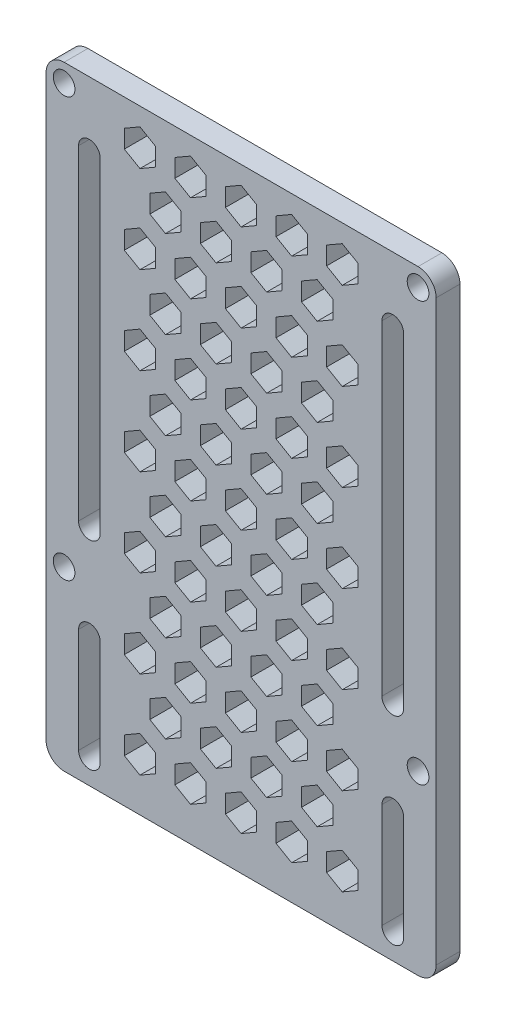
SolidWorks part; units mm, degrees
ref_plane "前基準面" through (0, 0, 0) normal (0, 0, 1) x (1, 0, 0)
ref_plane "上基準面" through (0, 0, 0) normal (0, 1, 0) x (1, 0, 0)
ref_plane "右基準面" through (0, 0, 0) normal (1, 0, 0) x (0, 0, -1)
sketch "草圖1" plane through (0, 0, 0) normal (0, 0, 1) x (1, 0, 0)
  line L0 (-16.3018, 23.2899) -> (-16.3018, -21.7101) construction
  line L1 (-19.8018, 29.7899) -> (29.1982, 29.7899) construction
  line L2 (-19.8018, 29.7899) -> (-19.8018, -28.2101) construction
  line L3 (-19.8018, -28.2101) -> (29.1982, -28.2101) construction
  line L4 (29.1982, 29.7899) -> (29.1982, -28.2101) construction
  line L5 (4.6982, 29.7899) -> (4.6982, 10.4942) construction
  line L6 (-20.7626, 0.7899) -> (-12.2996, 0.7899) construction
  line L7 (-16.3018, 29.7899) -> (-16.3018, 22.2296) construction
  line L8 (25.6982, 29.7899) -> (25.6982, 22.2296) construction
  line L9 (-14.8018, 23.2899) -> (-14.8018, -21.7101)
  line L10 (-17.8018, 23.2899) -> (-17.8018, -21.7101)
  line L11 (25.6982, 23.2899) -> (25.6982, -21.7101) construction
  line L12 (24.1982, 23.2899) -> (24.1982, -21.7101)
  line L13 (27.1982, 23.2899) -> (27.1982, -21.7101)
  line L14 (-19.8018, 32.2899) -> (29.1982, 32.2899)
  line L15 (-22.3018, 29.7899) -> (-22.3018, -28.2101)
  line L16 (31.6982, 29.7899) -> (31.6982, -28.2101)
  line L17 (-22.3018, -28.2101) -> (-22.3018, -50.2101)
  line L18 (-19.8018, -52.7101) -> (29.1982, -52.7101)
  line L19 (31.6982, -28.2101) -> (31.6982, -50.2101)
  line L20 (-16.3018, -34.7101) -> (-16.3018, -49.2101) construction
  line L21 (-14.8018, -34.7101) -> (-14.8018, -49.2101)
  line L22 (-17.8018, -34.7101) -> (-17.8018, -49.2101)
  line L23 (25.6982, -34.7101) -> (25.6982, -49.2101) construction
  line L24 (24.1982, -34.7101) -> (24.1982, -49.2101)
  line L25 (27.1982, -34.7101) -> (27.1982, -49.2101)
  line L26 (4.6982, 27.2899) -> (12.1639, 27.2899) construction
  line L27 (6.8632, 28.5399) -> (4.6982, 29.7899)
  line L28 (4.6982, 29.7899) -> (2.5331, 28.5399)
  line L29 (2.5331, 28.5399) -> (2.5331, 26.0399)
  line L30 (2.5331, 26.0399) -> (4.6982, 24.7899)
  line L31 (4.6982, 24.7899) -> (6.8632, 26.0399)
  line L32 (6.8632, 26.0399) -> (6.8632, 28.5399)
  line L33 (13.8632, 28.5399) -> (11.6982, 29.7899)
  line L34 (11.6982, 29.7899) -> (9.5331, 28.5399)
  line L35 (9.5331, 28.5399) -> (9.5331, 26.0399)
  line L36 (9.5331, 26.0399) -> (11.6982, 24.7899)
  line L37 (11.6982, 24.7899) -> (13.8632, 26.0399)
  line L38 (13.8632, 26.0399) -> (13.8632, 28.5399)
  line L39 (20.8632, 28.5399) -> (18.6982, 29.7899)
  line L40 (18.6982, 29.7899) -> (16.5331, 28.5399)
  line L41 (16.5331, 28.5399) -> (16.5331, 26.0399)
  line L42 (16.5331, 26.0399) -> (18.6982, 24.7899)
  line L43 (18.6982, 24.7899) -> (20.8632, 26.0399)
  line L44 (20.8632, 26.0399) -> (20.8632, 28.5399)
  line L45 (-0.1368, 28.5399) -> (-2.3018, 29.7899)
  line L46 (-2.3018, 29.7899) -> (-4.4669, 28.5399)
  line L47 (-4.4669, 28.5399) -> (-4.4669, 26.0399)
  line L48 (-4.4669, 26.0399) -> (-2.3018, 24.7899)
  line L49 (-2.3018, 24.7899) -> (-0.1368, 26.0399)
  line L50 (-0.1368, 26.0399) -> (-0.1368, 28.5399)
  line L51 (-7.1368, 28.5399) -> (-9.3018, 29.7899)
  line L52 (-9.3018, 29.7899) -> (-11.4669, 28.5399)
  line L53 (-11.4669, 28.5399) -> (-11.4669, 26.0399)
  line L54 (-11.4669, 26.0399) -> (-9.3018, 24.7899)
  line L55 (-9.3018, 24.7899) -> (-7.1368, 26.0399)
  line L56 (-7.1368, 26.0399) -> (-7.1368, 28.5399)
  line L57 (-2.3018, 24.7899) -> (4.6982, 24.7899) construction
  line L58 (1.229, 24.4101) -> (1.229, 20.9719) construction
  line L59 (10.3941, 19.9954) -> (10.3941, 22.4954)
  line L60 (3.3941, 19.9954) -> (3.3941, 22.4954)
  line L61 (3.3941, 22.4954) -> (1.229, 23.7454)
  line L62 (1.229, 23.7454) -> (-0.936, 22.4954)
  line L63 (-0.936, 22.4954) -> (-0.936, 19.9954)
  line L64 (-0.936, 19.9954) -> (1.229, 18.7454)
  line L65 (1.229, 18.7454) -> (3.3941, 19.9954)
  line L66 (10.3941, 22.4954) -> (8.229, 23.7454)
  line L67 (8.229, 23.7454) -> (6.064, 22.4954)
  line L68 (6.064, 22.4954) -> (6.064, 19.9954)
  line L69 (6.064, 19.9954) -> (8.229, 18.7454)
  line L70 (8.229, 18.7454) -> (10.3941, 19.9954)
  line L71 (17.3941, 19.9954) -> (17.3941, 22.4954)
  line L72 (17.3941, 22.4954) -> (15.229, 23.7454)
  line L73 (15.229, 23.7454) -> (13.064, 22.4954)
  line L74 (13.064, 22.4954) -> (13.064, 19.9954)
  line L75 (13.064, 19.9954) -> (15.229, 18.7454)
  line L76 (15.229, 18.7454) -> (17.3941, 19.9954)
  line L77 (-3.6059, 20.0151) -> (-3.6059, 22.5151)
  line L78 (-3.6059, 22.5151) -> (-5.7709, 23.7651)
  line L79 (-5.7709, 23.7651) -> (-7.936, 22.5151)
  line L80 (-7.936, 22.5151) -> (-7.936, 20.0151)
  line L81 (-7.936, 20.0151) -> (-5.7709, 18.7651)
  line L82 (-5.7709, 18.7651) -> (-3.6059, 20.0151)
  line L83 (-7.1368, 16.4152) -> (-9.3018, 17.6652)
  line L84 (-9.3018, 17.6652) -> (-11.4669, 16.4152)
  line L85 (-11.4669, 16.4152) -> (-11.4669, 13.9152)
  line L86 (-11.4669, 13.9152) -> (-9.3018, 12.6652)
  line L87 (-9.3018, 12.6652) -> (-7.1368, 13.9152)
  line L88 (-7.1368, 13.9152) -> (-7.1368, 16.4152)
  line L89 (-3.6059, 7.8905) -> (-3.6059, 10.3905)
  line L90 (-3.6059, 10.3905) -> (-5.7709, 11.6405)
  line L91 (-5.7709, 11.6405) -> (-7.936, 10.3905)
  line L92 (-7.936, 10.3905) -> (-7.936, 7.8905)
  line L93 (-7.936, 7.8905) -> (-5.7709, 6.6405)
  line L94 (-5.7709, 6.6405) -> (-3.6059, 7.8905)
  line L95 (-0.1368, 16.4152) -> (-2.3018, 17.6652)
  line L96 (-2.3018, 17.6652) -> (-4.4669, 16.4152)
  line L97 (-4.4669, 16.4152) -> (-4.4669, 13.9152)
  line L98 (-4.4669, 13.9152) -> (-2.3018, 12.6652)
  line L99 (-2.3018, 12.6652) -> (-0.1368, 13.9152)
  line L100 (-0.1368, 13.9152) -> (-0.1368, 16.4152)
  line L101 (3.3941, 7.8707) -> (3.3941, 10.3707)
  line L102 (3.3941, 10.3707) -> (1.229, 11.6207)
  line L103 (1.229, 11.6207) -> (-0.936, 10.3707)
  line L104 (-0.936, 10.3707) -> (-0.936, 7.8707)
  line L105 (-0.936, 7.8707) -> (1.229, 6.6207)
  line L106 (1.229, 6.6207) -> (3.3941, 7.8707)
  line L107 (6.8632, 16.4152) -> (4.6982, 17.6652)
  line L108 (4.6982, 17.6652) -> (2.5331, 16.4152)
  line L109 (2.5331, 16.4152) -> (2.5331, 13.9152)
  line L110 (2.5331, 13.9152) -> (4.6982, 12.6652)
  line L111 (4.6982, 12.6652) -> (6.8632, 13.9152)
  line L112 (6.8632, 13.9152) -> (6.8632, 16.4152)
  line L113 (13.8632, 16.4152) -> (11.6982, 17.6652)
  line L114 (11.6982, 17.6652) -> (9.5331, 16.4152)
  line L115 (9.5331, 16.4152) -> (9.5331, 13.9152)
  line L116 (9.5331, 13.9152) -> (11.6982, 12.6652)
  line L117 (11.6982, 12.6652) -> (13.8632, 13.9152)
  line L118 (13.8632, 13.9152) -> (13.8632, 16.4152)
  line L119 (20.8632, 16.4152) -> (18.6982, 17.6652)
  line L120 (18.6982, 17.6652) -> (16.5331, 16.4152)
  line L121 (16.5331, 16.4152) -> (16.5331, 13.9152)
  line L122 (16.5331, 13.9152) -> (18.6982, 12.6652)
  line L123 (18.6982, 12.6652) -> (20.8632, 13.9152)
  line L124 (20.8632, 13.9152) -> (20.8632, 16.4152)
  line L125 (17.3941, 7.8707) -> (17.3941, 10.3707)
  line L126 (17.3941, 10.3707) -> (15.229, 11.6207)
  line L127 (15.229, 11.6207) -> (13.064, 10.3707)
  line L128 (13.064, 10.3707) -> (13.064, 7.8707)
  line L129 (13.064, 7.8707) -> (15.229, 6.6207)
  line L130 (15.229, 6.6207) -> (17.3941, 7.8707)
  line L131 (10.3941, 7.8707) -> (10.3941, 10.3707)
  line L132 (10.3941, 10.3707) -> (8.229, 11.6207)
  line L133 (8.229, 11.6207) -> (6.064, 10.3707)
  line L134 (6.064, 10.3707) -> (6.064, 7.8707)
  line L135 (6.064, 7.8707) -> (8.229, 6.6207)
  line L136 (8.229, 6.6207) -> (10.3941, 7.8707)
  line L137 (-3.6059, -4.2295) -> (-3.6059, -1.7295)
  line L138 (-3.6059, -1.7295) -> (-5.7709, -0.4795)
  line L139 (-5.7709, -0.4795) -> (-7.936, -1.7295)
  line L140 (-7.936, -1.7295) -> (-7.936, -4.2295)
  line L141 (-7.936, -4.2295) -> (-5.7709, -5.4795)
  line L142 (-5.7709, -5.4795) -> (-3.6059, -4.2295)
  line L143 (-7.1368, 4.2952) -> (-9.3018, 5.5452)
  line L144 (-9.3018, 5.5452) -> (-11.4669, 4.2952)
  line L145 (-11.4669, 4.2952) -> (-11.4669, 1.7952)
  line L146 (-11.4669, 1.7952) -> (-9.3018, 0.5452)
  line L147 (-9.3018, 0.5452) -> (-7.1368, 1.7952)
  line L148 (-7.1368, 1.7952) -> (-7.1368, 4.2952)
  line L149 (-0.1368, 4.2952) -> (-2.3018, 5.5452)
  line L150 (-2.3018, 5.5452) -> (-4.4669, 4.2952)
  line L151 (-4.4669, 4.2952) -> (-4.4669, 1.7952)
  line L152 (-4.4669, 1.7952) -> (-2.3018, 0.5452)
  line L153 (-2.3018, 0.5452) -> (-0.1368, 1.7952)
  line L154 (-0.1368, 1.7952) -> (-0.1368, 4.2952)
  line L155 (3.3941, -4.2493) -> (3.3941, -1.7493)
  line L156 (3.3941, -1.7493) -> (1.229, -0.4993)
  line L157 (1.229, -0.4993) -> (-0.936, -1.7493)
  line L158 (-0.936, -1.7493) -> (-0.936, -4.2493)
  line L159 (-0.936, -4.2493) -> (1.229, -5.4993)
  line L160 (1.229, -5.4993) -> (3.3941, -4.2493)
  line L161 (10.3941, -4.2493) -> (10.3941, -1.7493)
  line L162 (10.3941, -1.7493) -> (8.229, -0.4993)
  line L163 (8.229, -0.4993) -> (6.064, -1.7493)
  line L164 (6.064, -1.7493) -> (6.064, -4.2493)
  line L165 (6.064, -4.2493) -> (8.229, -5.4993)
  line L166 (8.229, -5.4993) -> (10.3941, -4.2493)
  line L167 (6.8632, 4.2952) -> (4.6982, 5.5452)
  line L168 (4.6982, 5.5452) -> (2.5331, 4.2952)
  line L169 (2.5331, 4.2952) -> (2.5331, 1.7952)
  line L170 (2.5331, 1.7952) -> (4.6982, 0.5452)
  line L171 (4.6982, 0.5452) -> (6.8632, 1.7952)
  line L172 (6.8632, 1.7952) -> (6.8632, 4.2952)
  line L173 (13.8632, 4.2952) -> (11.6982, 5.5452)
  line L174 (11.6982, 5.5452) -> (9.5331, 4.2952)
  line L175 (9.5331, 4.2952) -> (9.5331, 1.7952)
  line L176 (9.5331, 1.7952) -> (11.6982, 0.5452)
  line L177 (11.6982, 0.5452) -> (13.8632, 1.7952)
  line L178 (13.8632, 1.7952) -> (13.8632, 4.2952)
  line L179 (20.8632, 4.2952) -> (18.6982, 5.5452)
  line L180 (18.6982, 5.5452) -> (16.5331, 4.2952)
  line L181 (16.5331, 4.2952) -> (16.5331, 1.7952)
  line L182 (16.5331, 1.7952) -> (18.6982, 0.5452)
  line L183 (18.6982, 0.5452) -> (20.8632, 1.7952)
  line L184 (20.8632, 1.7952) -> (20.8632, 4.2952)
  line L185 (17.3941, -4.2493) -> (17.3941, -1.7493)
  line L186 (17.3941, -1.7493) -> (15.229, -0.4993)
  line L187 (15.229, -0.4993) -> (13.064, -1.7493)
  line L188 (13.064, -1.7493) -> (13.064, -4.2493)
  line L189 (13.064, -4.2493) -> (15.229, -5.4993)
  line L190 (15.229, -5.4993) -> (17.3941, -4.2493)
  line L191 (-3.6059, -16.3495) -> (-3.6059, -13.8495)
  line L192 (-3.6059, -13.8495) -> (-5.7709, -12.5995)
  line L193 (-5.7709, -12.5995) -> (-7.936, -13.8495)
  line L194 (-7.936, -13.8495) -> (-7.936, -16.3495)
  line L195 (-7.936, -16.3495) -> (-5.7709, -17.5995)
  line L196 (-5.7709, -17.5995) -> (-3.6059, -16.3495)
  line L197 (-7.1368, -7.8248) -> (-9.3018, -6.5748)
  line L198 (-9.3018, -6.5748) -> (-11.4669, -7.8248)
  line L199 (-11.4669, -7.8248) -> (-11.4669, -10.3248)
  line L200 (-11.4669, -10.3248) -> (-9.3018, -11.5748)
  line L201 (-9.3018, -11.5748) -> (-7.1368, -10.3248)
  line L202 (-7.1368, -10.3248) -> (-7.1368, -7.8248)
  line L203 (-0.1368, -7.8248) -> (-2.3018, -6.5748)
  line L204 (-2.3018, -6.5748) -> (-4.4669, -7.8248)
  line L205 (-4.4669, -7.8248) -> (-4.4669, -10.3248)
  line L206 (-4.4669, -10.3248) -> (-2.3018, -11.5748)
  line L207 (-2.3018, -11.5748) -> (-0.1368, -10.3248)
  line L208 (-0.1368, -10.3248) -> (-0.1368, -7.8248)
  line L209 (3.3941, -16.3693) -> (3.3941, -13.8693)
  line L210 (3.3941, -13.8693) -> (1.229, -12.6193)
  line L211 (1.229, -12.6193) -> (-0.936, -13.8693)
  line L212 (-0.936, -13.8693) -> (-0.936, -16.3693)
  line L213 (-0.936, -16.3693) -> (1.229, -17.6193)
  line L214 (1.229, -17.6193) -> (3.3941, -16.3693)
  line L215 (10.3941, -16.3693) -> (10.3941, -13.8693)
  line L216 (10.3941, -13.8693) -> (8.229, -12.6193)
  line L217 (8.229, -12.6193) -> (6.064, -13.8693)
  line L218 (6.064, -13.8693) -> (6.064, -16.3693)
  line L219 (6.064, -16.3693) -> (8.229, -17.6193)
  line L220 (8.229, -17.6193) -> (10.3941, -16.3693)
  line L221 (6.8632, -7.8248) -> (4.6982, -6.5748)
  line L222 (4.6982, -6.5748) -> (2.5331, -7.8248)
  line L223 (2.5331, -7.8248) -> (2.5331, -10.3248)
  line L224 (2.5331, -10.3248) -> (4.6982, -11.5748)
  line L225 (4.6982, -11.5748) -> (6.8632, -10.3248)
  line L226 (6.8632, -10.3248) -> (6.8632, -7.8248)
  line L227 (13.8632, -7.8248) -> (11.6982, -6.5748)
  line L228 (11.6982, -6.5748) -> (9.5331, -7.8248)
  line L229 (9.5331, -7.8248) -> (9.5331, -10.3248)
  line L230 (9.5331, -10.3248) -> (11.6982, -11.5748)
  line L231 (11.6982, -11.5748) -> (13.8632, -10.3248)
  line L232 (13.8632, -10.3248) -> (13.8632, -7.8248)
  line L233 (20.8632, -7.8248) -> (18.6982, -6.5748)
  line L234 (18.6982, -6.5748) -> (16.5331, -7.8248)
  line L235 (16.5331, -7.8248) -> (16.5331, -10.3248)
  line L236 (16.5331, -10.3248) -> (18.6982, -11.5748)
  line L237 (18.6982, -11.5748) -> (20.8632, -10.3248)
  line L238 (20.8632, -10.3248) -> (20.8632, -7.8248)
  line L239 (17.3941, -16.3693) -> (17.3941, -13.8693)
  line L240 (17.3941, -13.8693) -> (15.229, -12.6193)
  line L241 (15.229, -12.6193) -> (13.064, -13.8693)
  line L242 (13.064, -13.8693) -> (13.064, -16.3693)
  line L243 (13.064, -16.3693) -> (15.229, -17.6193)
  line L244 (15.229, -17.6193) -> (17.3941, -16.3693)
  line L245 (-3.6059, -28.4695) -> (-3.6059, -25.9695)
  line L246 (-3.6059, -25.9695) -> (-5.7709, -24.7195)
  line L247 (-5.7709, -24.7195) -> (-7.936, -25.9695)
  line L248 (-7.936, -25.9695) -> (-7.936, -28.4695)
  line L249 (-7.936, -28.4695) -> (-5.7709, -29.7195)
  line L250 (-5.7709, -29.7195) -> (-3.6059, -28.4695)
  line L251 (-7.1368, -19.9448) -> (-9.3018, -18.6948)
  line L252 (-9.3018, -18.6948) -> (-11.4669, -19.9448)
  line L253 (-11.4669, -19.9448) -> (-11.4669, -22.4448)
  line L254 (-11.4669, -22.4448) -> (-9.3018, -23.6948)
  line L255 (-9.3018, -23.6948) -> (-7.1368, -22.4448)
  line L256 (-7.1368, -22.4448) -> (-7.1368, -19.9448)
  line L257 (-0.1368, -19.9448) -> (-2.3018, -18.6948)
  line L258 (-2.3018, -18.6948) -> (-4.4669, -19.9448)
  line L259 (-4.4669, -19.9448) -> (-4.4669, -22.4448)
  line L260 (-4.4669, -22.4448) -> (-2.3018, -23.6948)
  line L261 (-2.3018, -23.6948) -> (-0.1368, -22.4448)
  line L262 (-0.1368, -22.4448) -> (-0.1368, -19.9448)
  line L263 (3.3941, -28.4893) -> (3.3941, -25.9893)
  line L264 (3.3941, -25.9893) -> (1.229, -24.7393)
  line L265 (1.229, -24.7393) -> (-0.936, -25.9893)
  line L266 (-0.936, -25.9893) -> (-0.936, -28.4893)
  line L267 (-0.936, -28.4893) -> (1.229, -29.7393)
  line L268 (1.229, -29.7393) -> (3.3941, -28.4893)
  line L269 (10.3941, -28.4893) -> (10.3941, -25.9893)
  line L270 (10.3941, -25.9893) -> (8.229, -24.7393)
  line L271 (8.229, -24.7393) -> (6.064, -25.9893)
  line L272 (6.064, -25.9893) -> (6.064, -28.4893)
  line L273 (6.064, -28.4893) -> (8.229, -29.7393)
  line L274 (8.229, -29.7393) -> (10.3941, -28.4893)
  line L275 (6.8632, -19.9448) -> (4.6982, -18.6948)
  line L276 (4.6982, -18.6948) -> (2.5331, -19.9448)
  line L277 (2.5331, -19.9448) -> (2.5331, -22.4448)
  line L278 (2.5331, -22.4448) -> (4.6982, -23.6948)
  line L279 (4.6982, -23.6948) -> (6.8632, -22.4448)
  line L280 (6.8632, -22.4448) -> (6.8632, -19.9448)
  line L281 (13.8632, -19.9448) -> (11.6982, -18.6948)
  line L282 (11.6982, -18.6948) -> (9.5331, -19.9448)
  line L283 (9.5331, -19.9448) -> (9.5331, -22.4448)
  line L284 (9.5331, -22.4448) -> (11.6982, -23.6948)
  line L285 (11.6982, -23.6948) -> (13.8632, -22.4448)
  line L286 (13.8632, -22.4448) -> (13.8632, -19.9448)
  line L287 (20.8632, -19.9448) -> (18.6982, -18.6948)
  line L288 (18.6982, -18.6948) -> (16.5331, -19.9448)
  line L289 (16.5331, -19.9448) -> (16.5331, -22.4448)
  line L290 (16.5331, -22.4448) -> (18.6982, -23.6948)
  line L291 (18.6982, -23.6948) -> (20.8632, -22.4448)
  line L292 (20.8632, -22.4448) -> (20.8632, -19.9448)
  line L293 (17.3941, -28.4893) -> (17.3941, -25.9893)
  line L294 (17.3941, -25.9893) -> (15.229, -24.7393)
  line L295 (15.229, -24.7393) -> (13.064, -25.9893)
  line L296 (13.064, -25.9893) -> (13.064, -28.4893)
  line L297 (13.064, -28.4893) -> (15.229, -29.7393)
  line L298 (15.229, -29.7393) -> (17.3941, -28.4893)
  line L299 (-3.6059, -40.5895) -> (-3.6059, -38.0895)
  line L300 (-3.6059, -38.0895) -> (-5.7709, -36.8395)
  line L301 (-5.7709, -36.8395) -> (-7.936, -38.0895)
  line L302 (-7.936, -38.0895) -> (-7.936, -40.5895)
  line L303 (-7.936, -40.5895) -> (-5.7709, -41.8395)
  line L304 (-5.7709, -41.8395) -> (-3.6059, -40.5895)
  line L305 (-7.1368, -32.0648) -> (-9.3018, -30.8148)
  line L306 (-9.3018, -30.8148) -> (-11.4669, -32.0648)
  line L307 (-11.4669, -32.0648) -> (-11.4669, -34.5648)
  line L308 (-11.4669, -34.5648) -> (-9.3018, -35.8148)
  line L309 (-9.3018, -35.8148) -> (-7.1368, -34.5648)
  line L310 (-7.1368, -34.5648) -> (-7.1368, -32.0648)
  line L311 (-0.1368, -32.0648) -> (-2.3018, -30.8148)
  line L312 (-2.3018, -30.8148) -> (-4.4669, -32.0648)
  line L313 (-4.4669, -32.0648) -> (-4.4669, -34.5648)
  line L314 (-4.4669, -34.5648) -> (-2.3018, -35.8148)
  line L315 (-2.3018, -35.8148) -> (-0.1368, -34.5648)
  line L316 (-0.1368, -34.5648) -> (-0.1368, -32.0648)
  line L317 (3.3941, -40.6093) -> (3.3941, -38.1093)
  line L318 (3.3941, -38.1093) -> (1.229, -36.8593)
  line L319 (1.229, -36.8593) -> (-0.936, -38.1093)
  line L320 (-0.936, -38.1093) -> (-0.936, -40.6093)
  line L321 (-0.936, -40.6093) -> (1.229, -41.8593)
  line L322 (1.229, -41.8593) -> (3.3941, -40.6093)
  line L323 (10.3941, -40.6093) -> (10.3941, -38.1093)
  line L324 (10.3941, -38.1093) -> (8.229, -36.8593)
  line L325 (8.229, -36.8593) -> (6.064, -38.1093)
  line L326 (6.064, -38.1093) -> (6.064, -40.6093)
  line L327 (6.064, -40.6093) -> (8.229, -41.8593)
  line L328 (8.229, -41.8593) -> (10.3941, -40.6093)
  line L329 (6.8632, -32.0648) -> (4.6982, -30.8148)
  line L330 (4.6982, -30.8148) -> (2.5331, -32.0648)
  line L331 (2.5331, -32.0648) -> (2.5331, -34.5648)
  line L332 (2.5331, -34.5648) -> (4.6982, -35.8148)
  line L333 (4.6982, -35.8148) -> (6.8632, -34.5648)
  line L334 (6.8632, -34.5648) -> (6.8632, -32.0648)
  line L335 (13.8632, -32.0648) -> (11.6982, -30.8148)
  line L336 (11.6982, -30.8148) -> (9.5331, -32.0648)
  line L337 (9.5331, -32.0648) -> (9.5331, -34.5648)
  line L338 (9.5331, -34.5648) -> (11.6982, -35.8148)
  line L339 (11.6982, -35.8148) -> (13.8632, -34.5648)
  line L340 (13.8632, -34.5648) -> (13.8632, -32.0648)
  line L341 (20.8632, -32.0648) -> (18.6982, -30.8148)
  line L342 (18.6982, -30.8148) -> (16.5331, -32.0648)
  line L343 (16.5331, -32.0648) -> (16.5331, -34.5648)
  line L344 (16.5331, -34.5648) -> (18.6982, -35.8148)
  line L345 (18.6982, -35.8148) -> (20.8632, -34.5648)
  line L346 (20.8632, -34.5648) -> (20.8632, -32.0648)
  line L347 (17.3941, -40.6093) -> (17.3941, -38.1093)
  line L348 (17.3941, -38.1093) -> (15.229, -36.8593)
  line L349 (15.229, -36.8593) -> (13.064, -38.1093)
  line L350 (13.064, -38.1093) -> (13.064, -40.6093)
  line L351 (13.064, -40.6093) -> (15.229, -41.8593)
  line L352 (15.229, -41.8593) -> (17.3941, -40.6093)
  line L353 (-7.1368, -44.1848) -> (-9.3018, -42.9348)
  line L354 (-9.3018, -42.9348) -> (-11.4669, -44.1848)
  line L355 (-11.4669, -44.1848) -> (-11.4669, -46.6848)
  line L356 (-11.4669, -46.6848) -> (-9.3018, -47.9348)
  line L357 (-9.3018, -47.9348) -> (-7.1368, -46.6848)
  line L358 (-7.1368, -46.6848) -> (-7.1368, -44.1848)
  line L359 (-0.1368, -44.1848) -> (-2.3018, -42.9348)
  line L360 (-2.3018, -42.9348) -> (-4.4669, -44.1848)
  line L361 (-4.4669, -44.1848) -> (-4.4669, -46.6848)
  line L362 (-4.4669, -46.6848) -> (-2.3018, -47.9348)
  line L363 (-2.3018, -47.9348) -> (-0.1368, -46.6848)
  line L364 (-0.1368, -46.6848) -> (-0.1368, -44.1848)
  line L365 (6.8632, -44.1848) -> (4.6982, -42.9348)
  line L366 (4.6982, -42.9348) -> (2.5331, -44.1848)
  line L367 (2.5331, -44.1848) -> (2.5331, -46.6848)
  line L368 (2.5331, -46.6848) -> (4.6982, -47.9348)
  line L369 (4.6982, -47.9348) -> (6.8632, -46.6848)
  line L370 (6.8632, -46.6848) -> (6.8632, -44.1848)
  line L371 (13.8632, -44.1848) -> (11.6982, -42.9348)
  line L372 (11.6982, -42.9348) -> (9.5331, -44.1848)
  line L373 (9.5331, -44.1848) -> (9.5331, -46.6848)
  line L374 (9.5331, -46.6848) -> (11.6982, -47.9348)
  line L375 (11.6982, -47.9348) -> (13.8632, -46.6848)
  line L376 (13.8632, -46.6848) -> (13.8632, -44.1848)
  line L377 (20.8632, -44.1848) -> (18.6982, -42.9348)
  line L378 (18.6982, -42.9348) -> (16.5331, -44.1848)
  line L379 (16.5331, -44.1848) -> (16.5331, -46.6848)
  line L380 (16.5331, -46.6848) -> (18.6982, -47.9348)
  line L381 (18.6982, -47.9348) -> (20.8632, -46.6848)
  line L382 (20.8632, -46.6848) -> (20.8632, -44.1848)
  circle A0 centre (-19.8018, 29.7899) radius 1.5
  circle A1 centre (29.1982, 29.7899) radius 1.5
  circle A2 centre (29.1982, -28.2101) radius 1.5
  circle A3 centre (-19.8018, -28.2101) radius 1.5
  arc A4 (-14.8018, 23.2899) -> (-17.8018, 23.2899) centre (-16.3018, 23.2899) ccw
  arc A5 (-17.8018, -21.7101) -> (-14.8018, -21.7101) centre (-16.3018, -21.7101) ccw
  arc A6 (24.1982, 23.2899) -> (27.1982, 23.2899) centre (25.6982, 23.2899) cw
  arc A7 (27.1982, -21.7101) -> (24.1982, -21.7101) centre (25.6982, -21.7101) cw
  arc A8 (-19.8018, 32.2899) -> (-22.3018, 29.7899) centre (-19.8018, 29.7899) ccw
  arc A11 (29.1982, 32.2899) -> (31.6982, 29.7899) centre (29.1982, 29.7899) cw
  arc A12 (-22.3018, -50.2101) -> (-19.8018, -52.7101) centre (-19.8018, -50.2101) ccw
  arc A13 (31.6982, -50.2101) -> (29.1982, -52.7101) centre (29.1982, -50.2101) cw
  arc A14 (-14.8018, -34.7101) -> (-17.8018, -34.7101) centre (-16.3018, -34.7101) ccw
  arc A15 (-17.8018, -49.2101) -> (-14.8018, -49.2101) centre (-16.3018, -49.2101) ccw
  arc A16 (24.1982, -34.7101) -> (27.1982, -34.7101) centre (25.6982, -34.7101) cw
  arc A17 (27.1982, -49.2101) -> (24.1982, -49.2101) centre (25.6982, -49.2101) cw
  circle A18 centre (4.6982, 27.2899) radius 2.1651 construction
  circle A19 centre (1.229, 21.2454) radius 2.1651 construction
  point P15 (4.6982, 29.7899)
  point P19 (-16.3018, 0.7899)
  point P28 (25.6982, 0.7899)
  point P47 (-16.3018, -41.9601)
  point P57 (25.6982, -41.9601)
  dimension "D3" = 21
  dimension "D4" = 6.5
  dimension "D5" = 3.5
  dimension "D1" = 58
  dimension "D2" = 49
  dimension "D6" = 3
  dimension "D8" = 2.67
  dimension "D9" = 3
  dimension "D12" = 2.67
  dimension "D13" = 5
  dimension "D7" = 3
  dimension "D10" = 2
  dimension "D11" = 2
  dimension "D14" = 2
extrude "填料-伸長1" add sketch "草圖1" along normal blind 3.3
